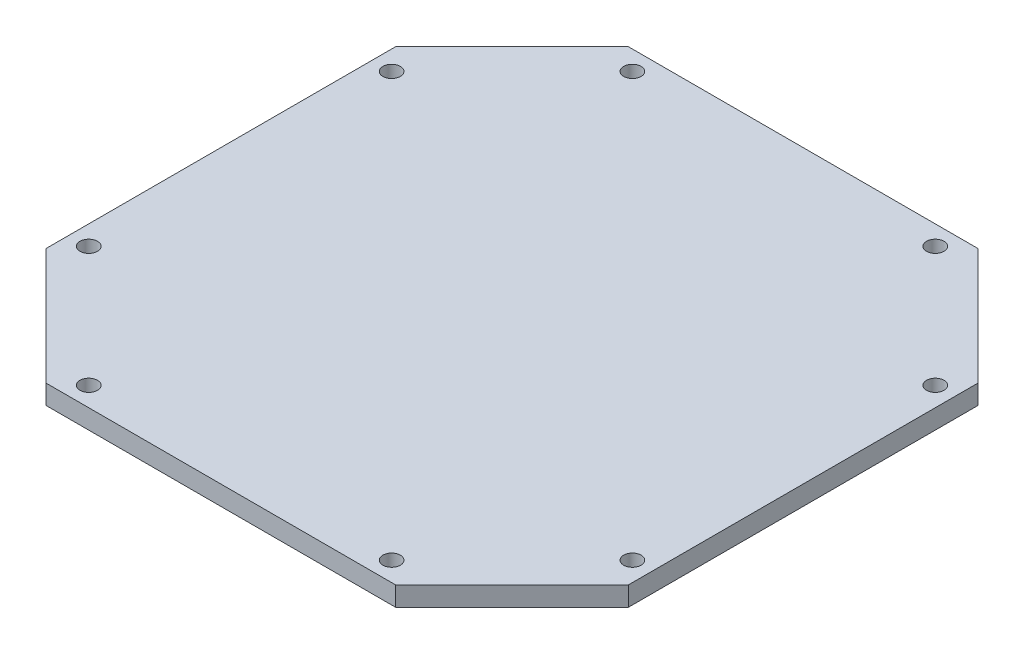
SolidWorks part; units mm, degrees
ref_plane "Front Plane" through (0, 0, 0) normal (0, 0, 1) x (1, 0, 0)
ref_plane "Top Plane" through (0, 0, 0) normal (0, 1, 0) x (1, 0, 0)
ref_plane "Right Plane" through (0, 0, 0) normal (1, 0, 0) x (0, 0, -1)
sketch "Sketch1" plane through (0, 0, 0) normal (0, 1, 0) x (1, 0, 0)
  line L0 (-146.0912, 90.4886) -> (-86.0912, 150.4886)
  line L1 (-86.0912, 150.4886) -> (93.9088, 150.4886)
  line L2 (-146.0912, 90.4886) -> (-146.0912, -89.5114)
  line L3 (-86.0912, -149.5114) -> (93.9088, -149.5114)
  line L4 (153.9088, 90.4886) -> (153.9088, -89.5114)
  line L5 (93.9088, 150.4886) -> (153.9088, 90.4886)
  line L6 (93.9088, -149.5114) -> (153.9088, -89.5114)
  line L7 (-146.0912, -89.5114) -> (-86.0912, -149.5114)
  point P0 (-146.0912, 150.4886)
  point P1 (153.9088, -149.5114)
  point P2 (-146.0912, -149.5114)
  point P3 (153.9088, 150.4886)
  dimension "D1" = 300
  dimension "D2" = 300
  dimension "D3" = 60
  dimension "D4" = 45
  dimension "D5" = 60
  dimension "D6" = 45
  dimension "D7" = 60
  dimension "D8" = 45
  dimension "D9" = 60
  dimension "D10" = 45
extrude "Boss-Extrude1" add sketch "Sketch1" along normal blind 10
sketch "Sketch2" plane through (0, 10, 0) normal (0, 1, 0) x (1, 0, 0)
  line L0 (-146.0912, 90.4886) -> (-146.0912, -89.5114) construction
  line L1 (-86.0912, -149.5114) -> (93.9088, -149.5114) construction
  line L2 (153.9088, -89.5114) -> (153.9088, 90.4886) construction
  line L3 (93.9088, 150.4886) -> (-86.0912, 150.4886) construction
  point P0 (-136.0912, 78.4886)
  point P2 (-74.0912, 140.4886)
  point P4 (81.9088, 140.4886)
  point P6 (143.9088, 78.4886)
  point P8 (143.9088, -77.5114)
  point P10 (81.9088, -139.5114)
  point P12 (-74.0912, -139.5114)
  point P14 (-136.0912, -77.5114)
  point P25 (0, 0)
  point P26 (0, 0)
  point P27 (0, 0)
  point P28 (0, 0)
  point P29 (0, 0)
  point P30 (0, 0)
  point P31 (0, 0)
  point P32 (0, 0)
  point P33 (0, 0)
  dimension "D1" = 10
  dimension "D2" = 10
  dimension "D3" = 10
  dimension "D4" = 10
  dimension "D5" = 280
  dimension "D6" = 62
  dimension "D7" = 218
  dimension "D8" = 156
  dimension "D9" = 72
  dimension "D10" = 218
  dimension "D11" = 62
hole_wizard "Ø1.0mm Dowel Hole1" positions "Sketch2" profile "Sketch3" hole size "Ø1.0" standard "ISO" end condition through all
sketch "Sketch3" plane through (-136.0912, 10, -78.4886) normal (1, 0, 0) x (0, 0, 1)
  line L0 (0, 0) -> (0, 10)
  line L1 (0, 10) -> (4.5, 10)
  line L2 (4.5, 10) -> (4.5, 0)
  line L5 (4.5, 0) -> (0, 0)
  line L11 (0, -6.35) -> (0, 107.95) construction
  dimension "Thru Hole Dia." = 9
  dimension "Thru Hole Depth" = 10
